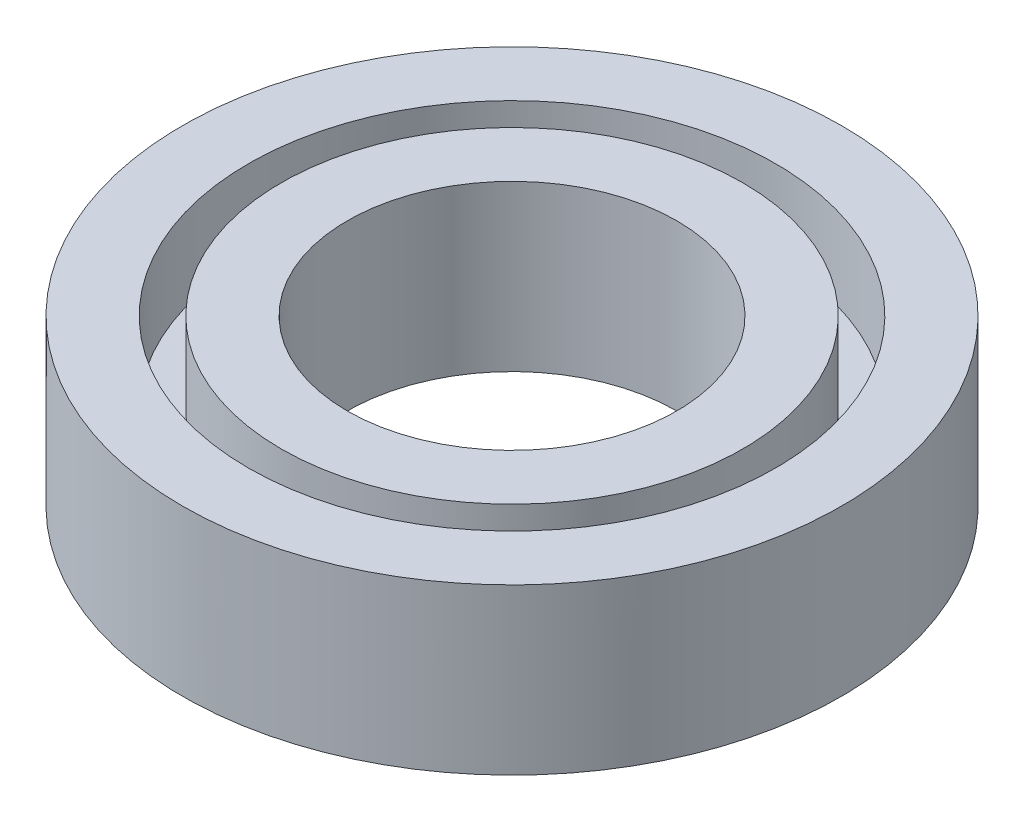
SolidWorks part; units mm, degrees
ref_plane "Front Plane" through (0, 0, 0) normal (0, 0, 1) x (1, 0, 0)
ref_plane "Top Plane" through (0, 0, 0) normal (0, 1, 0) x (1, 0, 0)
ref_plane "Right Plane" through (0, 0, 0) normal (1, 0, 0) x (0, 0, -1)
sketch "Sketch1" plane through (0, 0, 0) normal (0, 1, 0) x (1, 0, 0)
  circle A0 centre (0, 0) radius 2
  circle A1 centre (0, 0) radius 4
  dimension "D1" = 8
  dimension "D2" = 4
extrude "Boss-Extrude1" add sketch "Sketch1" along normal blind 3
sketch "Sketch2" plane through (0, 3, 0) normal (0, 1, 0) x (1, 0, 0)
  circle A2 centre (0, 0) radius 3.2
  circle A3 centre (0, 0) radius 3.2
  circle A5 centre (0, 0) radius 2.8
  circle A6 centre (0, 0) radius 2.8
  dimension "D1" = 0.8
  dimension "D2" = 0.8
extrude "Cut-Extrude1" cut sketch "Sketch2" against normal blind 1
sketch "Sketch3" plane through (0, 0, 0) normal (0, -1, 0) x (1, 0, 0)
  circle A2 centre (0, 0) radius 2
  circle A3 centre (0, 0) radius 2
  circle A5 centre (0, 0) radius 4
  circle A6 centre (0, 0) radius 4
  dimension "D1" = 2
  dimension "D2" = 2
extrude "Cut-Extrude2" cut sketch "Sketch3" against normal blind 1
